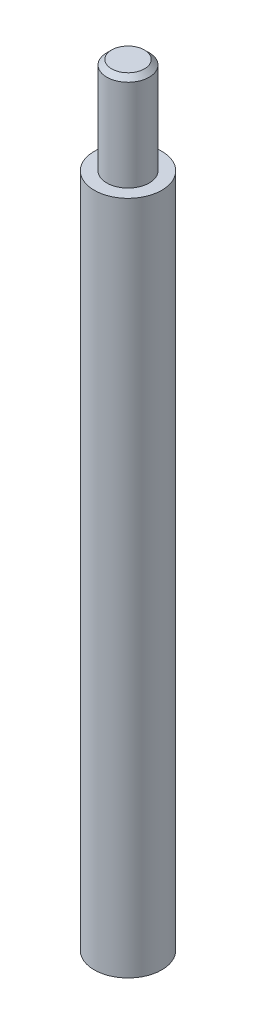
SolidWorks part; units mm, degrees
ref_plane "Front Plane" through (0, 0, 0) normal (0, 0, 1) x (1, 0, 0)
ref_plane "Top Plane" through (0, 0, 0) normal (0, 1, 0) x (1, 0, 0)
ref_plane "Right Plane" through (0, 0, 0) normal (1, 0, 0) x (0, 0, -1)
sketch "Sketch1" plane through (0, 0, 0) normal (0, 0, 1) x (1, 0, 0)
  line L0 (0, -495.7322) -> (0, 24290.876) construction
  line L1 (0, 45) -> (-2.2, 45)
  line L2 (-2.2, 45) -> (-2.2, 35)
  line L3 (-2.2, 35) -> (-3.5, 35)
  line L4 (-3.5, 35) -> (-3.5, -35)
  line L5 (-3.5, -35) -> (0, -35)
  line L6 (0, -35) -> (0, 45)
  point P11 (-3.5, 0)
  dimension "D1" = 2.2
  dimension "D2" = 3.5
  dimension "D3" = 70
  dimension "D4" = 10
revolve "Revolve1" add sketch "Sketch1" angle 360 about L0
chamfer "Chamfer1" distance 0.5 angle 45 1 edges at (2.2, 45, 0)
